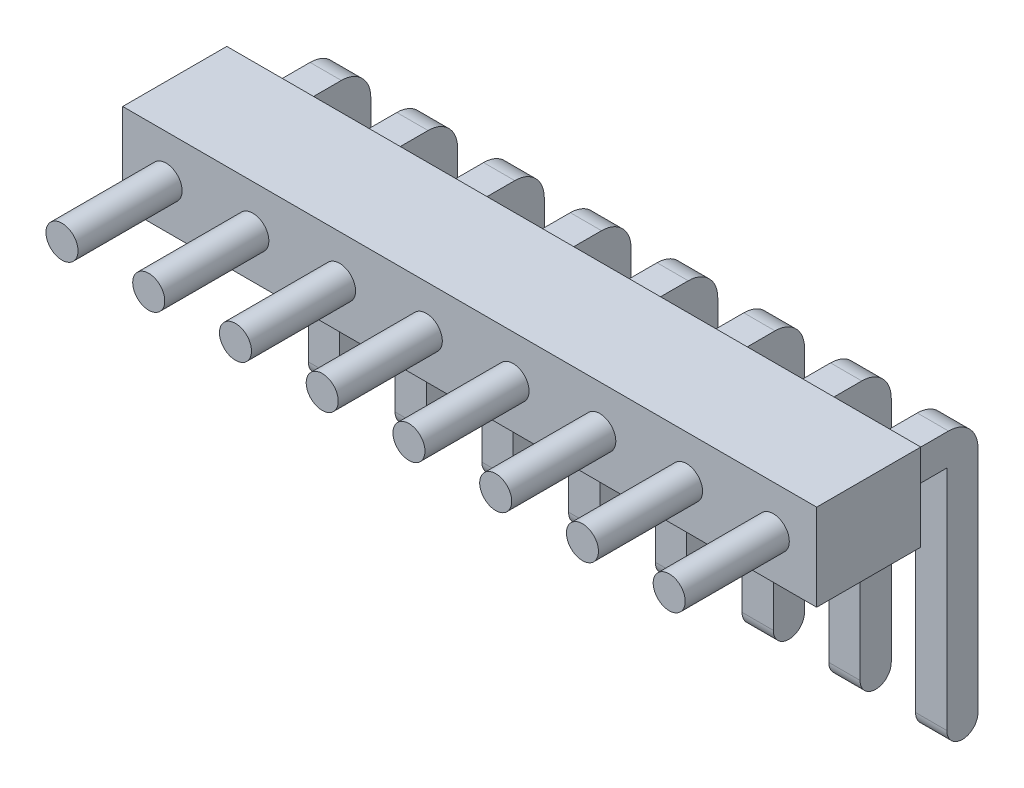
SolidWorks part; units mm, degrees
ref_plane "Alzado" through (0, 0, 0) normal (0, 0, 1) x (1, 0, 0)
ref_plane "Planta" through (0, 0, 0) normal (0, 1, 0) x (1, 0, 0)
ref_plane "Vista lateral" through (0, 0, 0) normal (1, 0, 0) x (0, 0, -1)
sketch "Croquis1" plane through (0, 0, 0) normal (0, 0, 1) x (1, 0, 0)
  line L0 (-10, 1.25) -> (10, 1.25)
  line L1 (-10, 1.25) -> (-10, -1.25)
  line L2 (-10, -1.25) -> (10, -1.25)
  line L3 (10, 1.25) -> (10, -1.25)
  line L4 (-10, 1.25) -> (10, -1.25) construction
  line L5 (-10, -1.25) -> (10, 1.25) construction
  point P0 (0, 0)
  dimension "D1" = 2.5
  dimension "D2" = 20
extrude "Saliente-Extruir1" add sketch "Croquis1" along normal blind 3
sketch "Croquis2" plane through (0, 0, 3) normal (0, 0, 1) x (1, 0, 0)
  line L0 (-10, 0) -> (-8.75, 0) construction
  line L1 (-10, 1.25) -> (-10, -1.25) construction
  line L7 (-9.2, 0.45) -> (-8.3, -0.45) construction
  line L8 (-9.2, -0.45) -> (-8.3, 0.45) construction
  circle A4 centre (-8.75, 0) radius 0.4616
  dimension "D1" = 1.25
  dimension "D2" = 0.9
  dimension "D3" = 0.9
extrude "Saliente-Extruir2" add sketch "Croquis2" along normal blind 3
pattern_linear "MatrizL1" count 8 spacing 2.5 along (1, 0, 0) of "Saliente-Extruir2"
ref_plane "Plano1" through (8.75, 0, 0) normal (1, 0, 0) x (0, 0, -1)
sketch "Croquis3" plane through (8.75, 0, 0) normal (1, 0, 0) x (0, 0, -1)
  line L0 (0, 0) -> (1.6, 0) construction
  line L1 (2, -0.4) -> (2, -7) construction
  line L2 (0, -0.45) -> (1.55, -0.45)
  line L3 (1.55, -0.45) -> (1.55, -7)
  line L4 (0, 0.45) -> (1.6, 0.45)
  line L5 (2.45, -0.4) -> (2.45, -7)
  line L6 (0, 0.45) -> (0, -0.45)
  arc A0 (1.6, 0) -> (2, -0.4) centre (1.6, -0.4) cw construction
  arc A1 (1.55, -0.45) -> (1.55, -0.45) centre (1.55, -0.45) cw
  arc A2 (1.6, 0.45) -> (2.45, -0.4) centre (1.6, -0.4) cw
  arc A4 (1.55, -7) -> (2.45, -7) centre (2, -7) ccw
  point P6 (2, 0)
  dimension "D3" = 0.4
  dimension "D1" = 2
  dimension "D2" = 7
  dimension "D4" = 0.45
  dimension "D5" = 0.45
extrude "Saliente-Extruir3" add sketch "Croquis3" along normal blind 0.45 and the other way blind 0.45
pattern_linear "MatrizL2" count 8 spacing 2.5 along (-1, 0, 0) of "Saliente-Extruir3"
